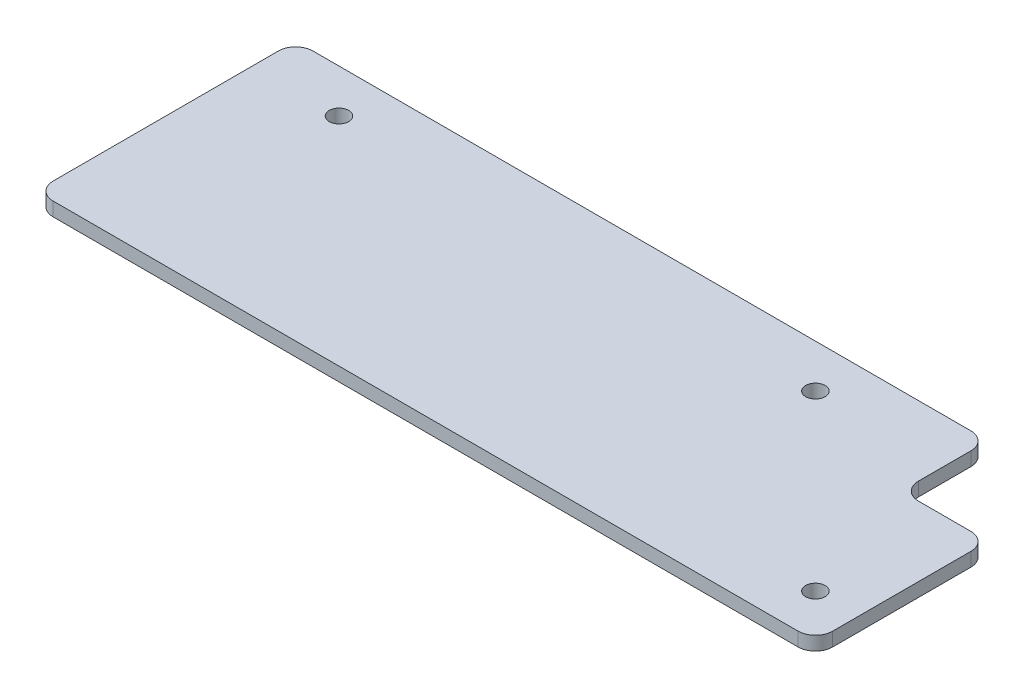
SolidWorks part; units mm, degrees
ref_plane "Front Plane" through (0, 0, 0) normal (0, 0, 1) x (1, 0, 0)
ref_plane "Top Plane" through (0, 0, 0) normal (0, 1, 0) x (1, 0, 0)
ref_plane "Right Plane" through (0, 0, 0) normal (1, 0, 0) x (0, 0, -1)
sketch "Sketch1" plane through (0, 0, 0) normal (0, 1, 0) x (1, 0, 0)
  line L1 (90, -30) -> (-90, -30)
  line L2 (90, -30) -> (90, 30)
  line L3 (90, 30) -> (-90, 30)
  line L4 (-90, -30) -> (-90, 30)
  line L5 (90, -30) -> (-90, 30) construction
  line L6 (90, 30) -> (-90, -30) construction
  point P0 (0, 0)
  dimension "D1" = 180
  dimension "D2" = 60
extrude "Boss-Extrude1" add sketch "Sketch1" along normal blind 3.175
sketch "Sketch2" plane through (0, 3.175, 0) normal (0, 1, 0) x (1, 0, 0)
  line L0 (90, 30) -> (-90, 30) construction
  line L2 (-90, 30) -> (-90, -30) construction
  line L3 (-90, -30) -> (90, -30) construction
  line L4 (90, -30) -> (90, 30) construction
  point P1 (80, -20)
  point P3 (40, 20)
  point P4 (-70, 20)
  dimension "D1" = 10
  dimension "D2" = 10
  dimension "D3" = 20
  dimension "D6" = 10
sketch "Sketch5" plane through (0, 3.175, 0) normal (0, 1, 0) x (1, 0, 0)
  line L0 (90, 30) -> (-90, 30) construction
  line L1 (69.9, 30) -> (90, 30)
  line L2 (69.9, 30) -> (69.9, 9.9)
  line L3 (69.9, 9.9) -> (90, 9.9)
  line L4 (90, 30) -> (90, 9.9)
  line L5 (90, -30) -> (90, 30) construction
  dimension "D1" = 20.1
  dimension "D2" = 20.1
extrude "Cut-Extrude1" cut sketch "Sketch5" against normal through all both and the other way through all
hole_wizard "M4 Clearance Hole2" positions "Sketch6" profile "Sketch7" hole size "M4" standard "ANSI Metric" end condition through all
sketch "Sketch6" plane through (0, 3.175, 0) normal (0, 1, 0) x (1, 0, 0)
  point P0 (-70, 20)
  point P3 (40, 20)
  point P6 (80, -20)
sketch "Sketch7" plane through (-70, 3.175, -20) normal (1, 0, 0) x (0, 0, 1)
  line L0 (0, 0) -> (0, 3.175)
  line L1 (0, 3.175) -> (2.25, 3.175)
  line L2 (2.25, 3.175) -> (2.25, 0)
  line L5 (2.25, 0) -> (0, 0)
  line L11 (0, -6.35) -> (0, 107.95) construction
  dimension "Thru Hole Dia." = 4.5
  dimension "Thru Hole Depth" = 3.175
fillet "Fillet2" radius 4 6 edges at (69.9, 1.5875, -30) (69.9, 1.5875, -9.9) (90, 1.5875, -9.9) (90, 1.5875, 30) (-90, 1.5875, -30) (-90, 1.5875, 30)
